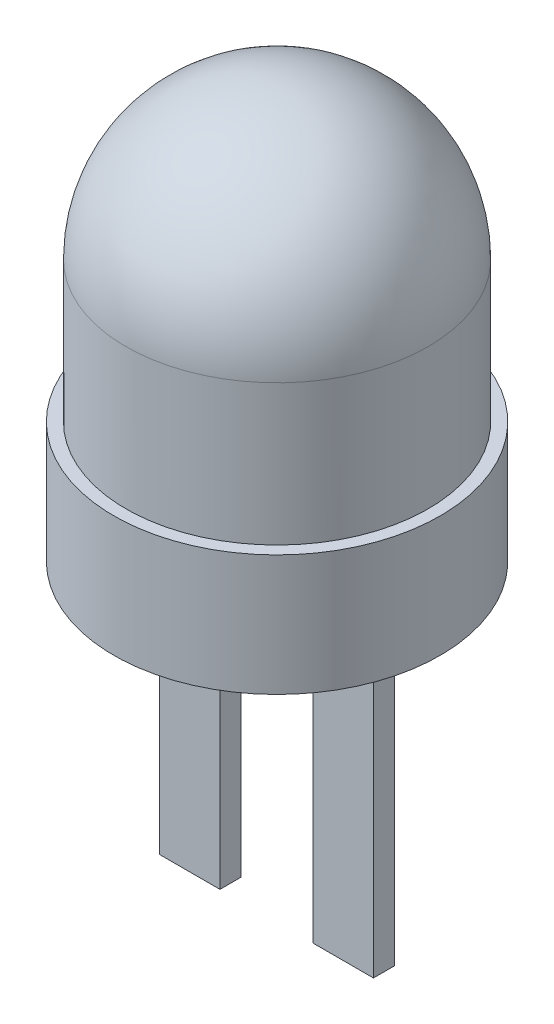
SolidWorks part; units mm, degrees
material "Acrylic (Medium-high impact)"
ref_plane "Front Plane" through (0, 0, 0) normal (0, 0, 1) x (1, 0, 0)
ref_plane "Top Plane" through (0, 0, 0) normal (0, 1, 0) x (1, 0, 0)
ref_plane "Right Plane" through (0, 0, 0) normal (1, 0, 0) x (0, 0, -1)
sketch "Sketch1" plane through (0, 0, 0) normal (0, 0, 1) x (1, 0, 0)
  line L0 (0, 0) -> (0, 6.825)
  line L1 (0, 0) -> (2.7, 0)
  line L2 (2.7, 0) -> (2.7, 2)
  line L3 (2.7, 2) -> (2.5, 2)
  line L4 (2.5, 2) -> (2.5, 4.325)
  arc A0 (2.5, 4.325) -> (0, 6.825) centre (0, 4.325) ccw
  dimension "D5" = 2.5
  dimension "D1" = 2.7
  dimension "D2" = 2.5
  dimension "D3" = 6.825
  dimension "D4" = 2
revolve "Revolve1" add sketch "Sketch1" angle 360 about L0
sketch "Sketch2" plane through (0, 0, 0) normal (0, -1, 0) x (1, 0, 0)
  line L0 (-1.77, 0) -> (-0.77, 0) construction
  line L1 (0.77, 0.175) -> (1.77, 0.175)
  line L2 (0.77, 0.175) -> (0.77, -0.175)
  line L3 (0.77, -0.175) -> (1.77, -0.175)
  line L4 (1.77, 0.175) -> (1.77, -0.175)
  line L5 (-0.77, 0.175) -> (-1.77, 0.175)
  line L6 (-0.77, 0.175) -> (-0.77, -0.175)
  line L7 (-0.77, -0.175) -> (-1.77, -0.175)
  line L8 (-1.77, 0.175) -> (-1.77, -0.175)
  line L9 (-0.77, 0) -> (0.77, 0) construction
  line L10 (0.77, 0) -> (1.77, 0) construction
  line L11 (-1.27, 0.175) -> (-1.27, -0.175) construction
  line L12 (1.27, 0.175) -> (1.27, -0.175) construction
  dimension "D1" = 0.35
  dimension "D2" = 1
  dimension "D3" = 2.54
extrude "Boss-Extrude1" add sketch "Sketch2" along normal blind 5 and the other way blind 5
